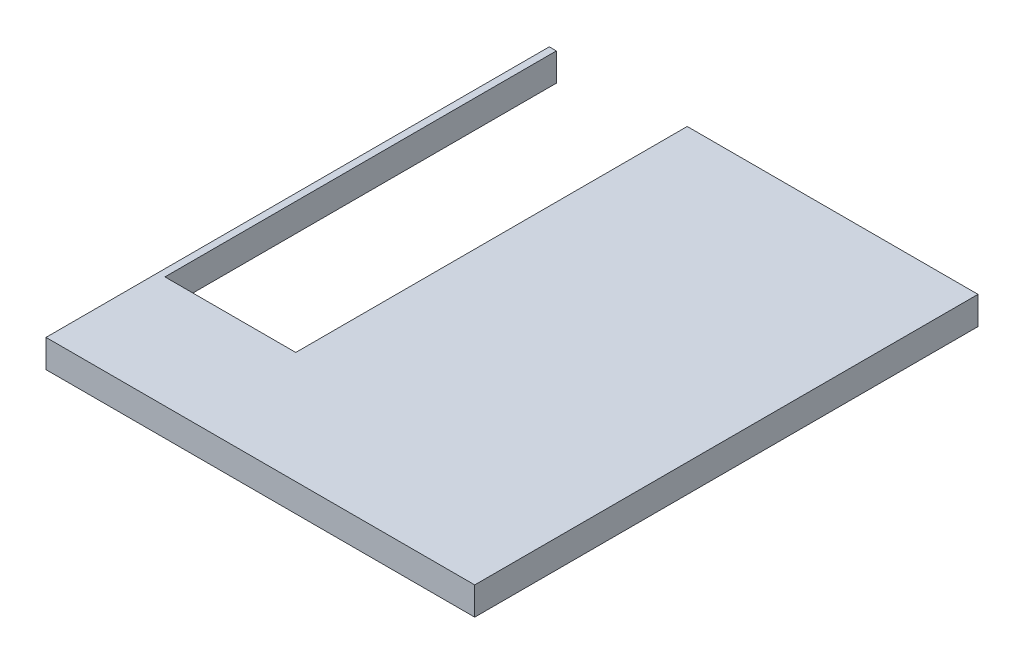
SolidWorks part; units mm, degrees
ref_plane "Plano frontal" through (0, 0, 0) normal (0, 0, 1) x (1, 0, 0)
ref_plane "Plano superior" through (0, 0, 0) normal (0, 1, 0) x (1, 0, 0)
ref_plane "Plano direito" through (0, 0, 0) normal (1, 0, 0) x (0, 0, -1)
sketch "Esboço1" plane through (0, 0, 0) normal (0, 0, 1) x (1, 0, 0)
  line L1 (0, 0) -> (2300, 0)
  line L2 (0, 0) -> (0, 150)
  line L3 (0, 150) -> (2300, 150)
  line L4 (2300, 0) -> (2300, 150)
  dimension "D1" = 150
  dimension "D2" = 2300
extrude "Ressalto-extrusão1" add sketch "Esboço1" along normal blind 2700
sketch "Esboço3" plane through (0, 150, 0) normal (0, 1, 0) x (1, 0, 0)
  line L0 (2300, 0) -> (0, 0) construction
  line L1 (740, -2100) -> (38, -2100)
  line L2 (740, -2100) -> (740, 0)
  line L3 (740, 0) -> (38, 0)
  line L4 (38, -2100) -> (38, 0)
  line L5 (0, -2700) -> (0, 0) construction
  dimension "D1" = 2100
  dimension "D2" = 38
  dimension "D3" = 702
extrude "PORTA" cut sketch "Esboço3" against normal through all
